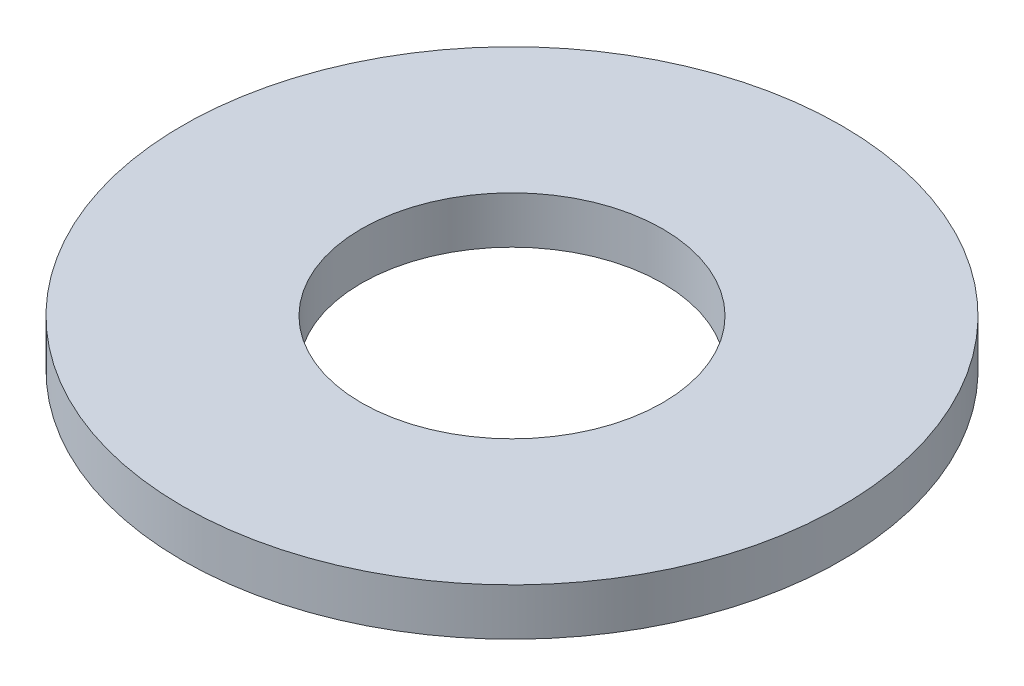
SolidWorks part; units mm, degrees
ref_plane "Alzado" through (0, 0, 0) normal (0, 0, 1) x (1, 0, 0)
ref_plane "Planta" through (0, 0, 0) normal (0, 1, 0) x (1, 0, 0)
ref_plane "Vista lateral" through (0, 0, 0) normal (1, 0, 0) x (0, 0, -1)
sketch "Croquis1" plane through (0, 0, 0) normal (0, 1, 0) x (1, 0, 0)
  circle A0 centre (0, 0) radius 1.6
  circle A1 centre (0, 0) radius 3.5
  dimension "D1" = 3.2
  dimension "D2" = 7
extrude "Saliente-Extruir1" add sketch "Croquis1" along normal blind 0.5
